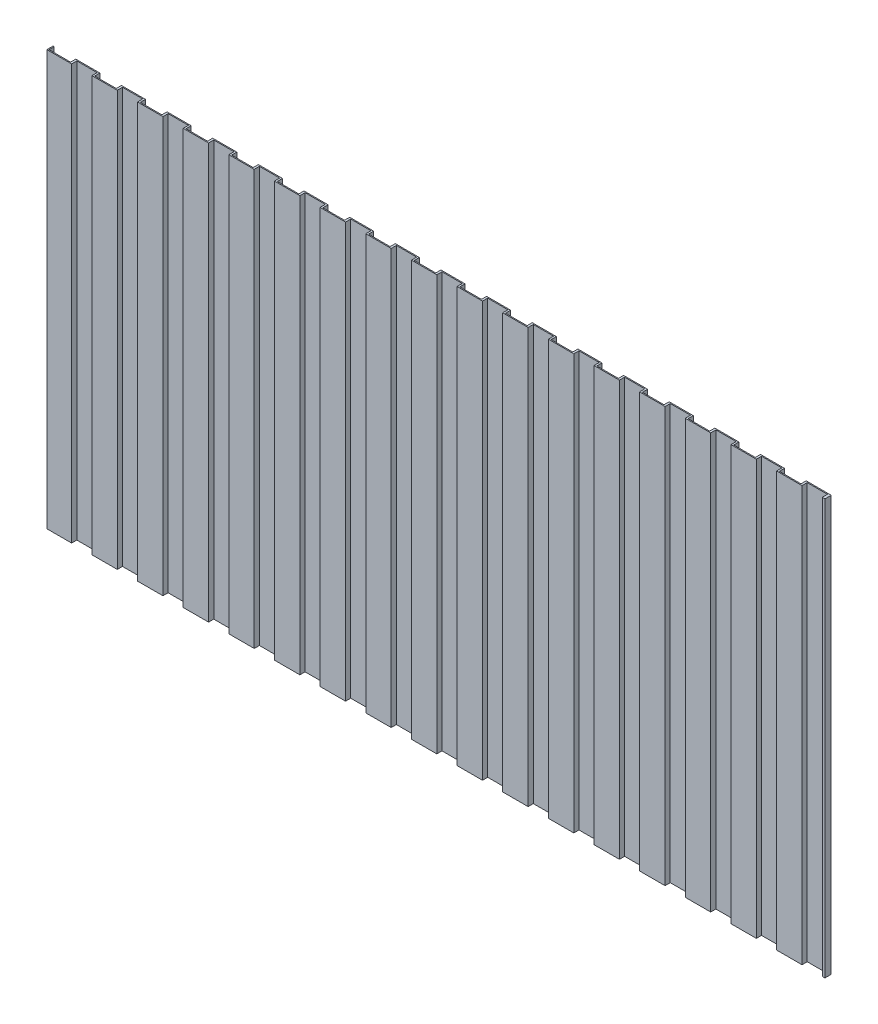
SolidWorks part; units mm, degrees
ref_plane "Front Plane" through (0, 0, 0) normal (0, 0, 1) x (1, 0, 0)
ref_plane "Top Plane" through (0, 0, 0) normal (0, 1, 0) x (1, 0, 0)
ref_plane "Right Plane" through (0, 0, 0) normal (1, 0, 0) x (0, 0, -1)
sketch "Sketch1" plane through (0, 0, 0) normal (0, 0, 1) x (1, 0, 0)
  line L1 (-3750, 2000) -> (3750, 2000)
  line L2 (-3750, 2000) -> (-3750, -2000)
  line L3 (-3750, -2000) -> (3750, -2000)
  line L4 (3750, 2000) -> (3750, -2000)
  line L5 (-3750, 2000) -> (3750, -2000) construction
  line L6 (-3750, -2000) -> (3750, 2000) construction
  point P0 (0, 0)
  dimension "D1" = 7500
  dimension "D2" = 4000
extrude "Boss-Extrude1" add sketch "Sketch1" along normal blind 60
sketch "Sketch2" plane through (0, -2000, 0) normal (0, -1, 0) x (-1, 0, 0)
  line L0 (3750, 0) -> (-3750, 0) construction
  line L1 (3739.0761, 0) -> (3531.0261, 0)
  line L2 (3739.0761, 0) -> (3739.0761, -50)
  line L3 (3739.0761, -50) -> (3531.0261, -50)
  line L4 (3531.0261, 0) -> (3531.0261, -50)
  line L5 (3750, -60) -> (-3750, -60) construction
  line L6 (3510.9951, -60) -> (3315.6922, -60)
  line L7 (3510.9951, -60) -> (3510.9951, -10)
  line L8 (3510.9951, -10) -> (3315.6922, -10)
  line L9 (3315.6922, -60) -> (3315.6922, -10)
  line L10 (3299.0761, -50) -> (3091.0261, -50)
  line L11 (3299.0761, 0) -> (3299.0761, -50)
  line L12 (3299.0761, 0) -> (3091.0261, 0)
  line L13 (3091.0261, 0) -> (3091.0261, -50)
  line L14 (3070.9951, -10) -> (2875.6922, -10)
  line L15 (3070.9951, -60) -> (3070.9951, -10)
  line L16 (3070.9951, -60) -> (2875.6922, -60)
  line L17 (2875.6922, -60) -> (2875.6922, -10)
  line L18 (2859.0761, -50) -> (2651.0261, -50)
  line L19 (2859.0761, 0) -> (2859.0761, -50)
  line L20 (2859.0761, 0) -> (2651.0261, 0)
  line L21 (2651.0261, 0) -> (2651.0261, -50)
  line L22 (2630.9951, -10) -> (2435.6922, -10)
  line L23 (2630.9951, -60) -> (2630.9951, -10)
  line L24 (2630.9951, -60) -> (2435.6922, -60)
  line L25 (2435.6922, -60) -> (2435.6922, -10)
  line L26 (2419.0761, -50) -> (2211.0261, -50)
  line L27 (2419.0761, 0) -> (2419.0761, -50)
  line L28 (2419.0761, 0) -> (2211.0261, 0)
  line L29 (2211.0261, 0) -> (2211.0261, -50)
  line L30 (2190.9951, -10) -> (1995.6922, -10)
  line L31 (2190.9951, -60) -> (2190.9951, -10)
  line L32 (2190.9951, -60) -> (1995.6922, -60)
  line L33 (1995.6922, -60) -> (1995.6922, -10)
  line L34 (1979.0761, -50) -> (1771.0261, -50)
  line L35 (1979.0761, 0) -> (1979.0761, -50)
  line L36 (1979.0761, 0) -> (1771.0261, 0)
  line L37 (1771.0261, 0) -> (1771.0261, -50)
  line L38 (1750.9951, -10) -> (1555.6922, -10)
  line L39 (1750.9951, -60) -> (1750.9951, -10)
  line L40 (1750.9951, -60) -> (1555.6922, -60)
  line L41 (1555.6922, -60) -> (1555.6922, -10)
  line L42 (1539.0761, -50) -> (1331.0261, -50)
  line L43 (1539.0761, 0) -> (1539.0761, -50)
  line L44 (1539.0761, 0) -> (1331.0261, 0)
  line L45 (1331.0261, 0) -> (1331.0261, -50)
  line L46 (1310.9951, -10) -> (1115.6922, -10)
  line L47 (1310.9951, -60) -> (1310.9951, -10)
  line L48 (1310.9951, -60) -> (1115.6922, -60)
  line L49 (1115.6922, -60) -> (1115.6922, -10)
  line L50 (1099.0761, -50) -> (891.0261, -50)
  line L51 (1099.0761, 0) -> (1099.0761, -50)
  line L52 (1099.0761, 0) -> (891.0261, 0)
  line L53 (891.0261, 0) -> (891.0261, -50)
  line L54 (870.9951, -10) -> (675.6922, -10)
  line L55 (870.9951, -60) -> (870.9951, -10)
  line L56 (870.9951, -60) -> (675.6922, -60)
  line L57 (675.6922, -60) -> (675.6922, -10)
  line L58 (659.0761, -50) -> (451.0261, -50)
  line L59 (659.0761, 0) -> (659.0761, -50)
  line L60 (659.0761, 0) -> (451.0261, 0)
  line L61 (451.0261, 0) -> (451.0261, -50)
  line L62 (430.9951, -10) -> (235.6922, -10)
  line L63 (430.9951, -60) -> (430.9951, -10)
  line L64 (430.9951, -60) -> (235.6922, -60)
  line L65 (235.6922, -60) -> (235.6922, -10)
  line L66 (219.0761, -50) -> (11.0261, -50)
  line L67 (219.0761, 0) -> (219.0761, -50)
  line L68 (219.0761, 0) -> (11.0261, 0)
  line L69 (11.0261, 0) -> (11.0261, -50)
  line L70 (-9.0049, -10) -> (-204.3078, -10)
  line L71 (-9.0049, -60) -> (-9.0049, -10)
  line L72 (-9.0049, -60) -> (-204.3078, -60)
  line L73 (-204.3078, -60) -> (-204.3078, -10)
  line L74 (-220.9239, -50) -> (-428.9739, -50)
  line L75 (-220.9239, 0) -> (-220.9239, -50)
  line L76 (-220.9239, 0) -> (-428.9739, 0)
  line L77 (-428.9739, 0) -> (-428.9739, -50)
  line L78 (-449.0049, -10) -> (-644.3078, -10)
  line L79 (-449.0049, -60) -> (-449.0049, -10)
  line L80 (-449.0049, -60) -> (-644.3078, -60)
  line L81 (-644.3078, -60) -> (-644.3078, -10)
  line L82 (-660.9239, -50) -> (-868.9739, -50)
  line L83 (-660.9239, 0) -> (-660.9239, -50)
  line L84 (-660.9239, 0) -> (-868.9739, 0)
  line L85 (-868.9739, 0) -> (-868.9739, -50)
  line L86 (-889.0049, -10) -> (-1084.3078, -10)
  line L87 (-889.0049, -60) -> (-889.0049, -10)
  line L88 (-889.0049, -60) -> (-1084.3078, -60)
  line L89 (-1084.3078, -60) -> (-1084.3078, -10)
  line L90 (-1100.9239, -50) -> (-1308.9739, -50)
  line L91 (-1100.9239, 0) -> (-1100.9239, -50)
  line L92 (-1100.9239, 0) -> (-1308.9739, 0)
  line L93 (-1308.9739, 0) -> (-1308.9739, -50)
  line L94 (-1329.0049, -10) -> (-1524.3078, -10)
  line L95 (-1329.0049, -60) -> (-1329.0049, -10)
  line L96 (-1329.0049, -60) -> (-1524.3078, -60)
  line L97 (-1524.3078, -60) -> (-1524.3078, -10)
  line L98 (-1540.9239, -50) -> (-1748.9739, -50)
  line L99 (-1540.9239, 0) -> (-1540.9239, -50)
  line L100 (-1540.9239, 0) -> (-1748.9739, 0)
  line L101 (-1748.9739, 0) -> (-1748.9739, -50)
  line L102 (-1769.0049, -10) -> (-1964.3078, -10)
  line L103 (-1769.0049, -60) -> (-1769.0049, -10)
  line L104 (-1769.0049, -60) -> (-1964.3078, -60)
  line L105 (-1964.3078, -60) -> (-1964.3078, -10)
  line L106 (-1980.9239, -50) -> (-2188.9739, -50)
  line L107 (-1980.9239, 0) -> (-1980.9239, -50)
  line L108 (-1980.9239, 0) -> (-2188.9739, 0)
  line L109 (-2188.9739, 0) -> (-2188.9739, -50)
  line L110 (-2209.0049, -10) -> (-2404.3078, -10)
  line L111 (-2209.0049, -60) -> (-2209.0049, -10)
  line L112 (-2209.0049, -60) -> (-2404.3078, -60)
  line L113 (-2404.3078, -60) -> (-2404.3078, -10)
  line L114 (-2420.9239, -50) -> (-2628.9739, -50)
  line L115 (-2420.9239, 0) -> (-2420.9239, -50)
  line L116 (-2420.9239, 0) -> (-2628.9739, 0)
  line L117 (-2628.9739, 0) -> (-2628.9739, -50)
  line L118 (-2649.0049, -10) -> (-2844.3078, -10)
  line L119 (-2649.0049, -60) -> (-2649.0049, -10)
  line L120 (-2649.0049, -60) -> (-2844.3078, -60)
  line L121 (-2844.3078, -60) -> (-2844.3078, -10)
  line L122 (-2860.9239, -50) -> (-3068.9739, -50)
  line L123 (-2860.9239, 0) -> (-2860.9239, -50)
  line L124 (-2860.9239, 0) -> (-3068.9739, 0)
  line L125 (-3068.9739, 0) -> (-3068.9739, -50)
  line L126 (-3089.0049, -10) -> (-3284.3078, -10)
  line L127 (-3089.0049, -60) -> (-3089.0049, -10)
  line L128 (-3089.0049, -60) -> (-3284.3078, -60)
  line L129 (-3284.3078, -60) -> (-3284.3078, -10)
  line L130 (-3300.9239, -50) -> (-3508.9739, -50)
  line L131 (-3300.9239, 0) -> (-3300.9239, -50)
  line L132 (-3300.9239, 0) -> (-3508.9739, 0)
  line L133 (-3508.9739, 0) -> (-3508.9739, -50)
  line L134 (-3529.0049, -10) -> (-3724.3078, -10)
  line L135 (-3529.0049, -60) -> (-3529.0049, -10)
  line L136 (-3529.0049, -60) -> (-3724.3078, -60)
  line L137 (-3724.3078, -60) -> (-3724.3078, -10)
  dimension "D1" = 10
  dimension "D2" = 10
  dimension "D3" = 17
extrude "Cut-Extrude1" cut sketch "Sketch2" against normal blind 5107
